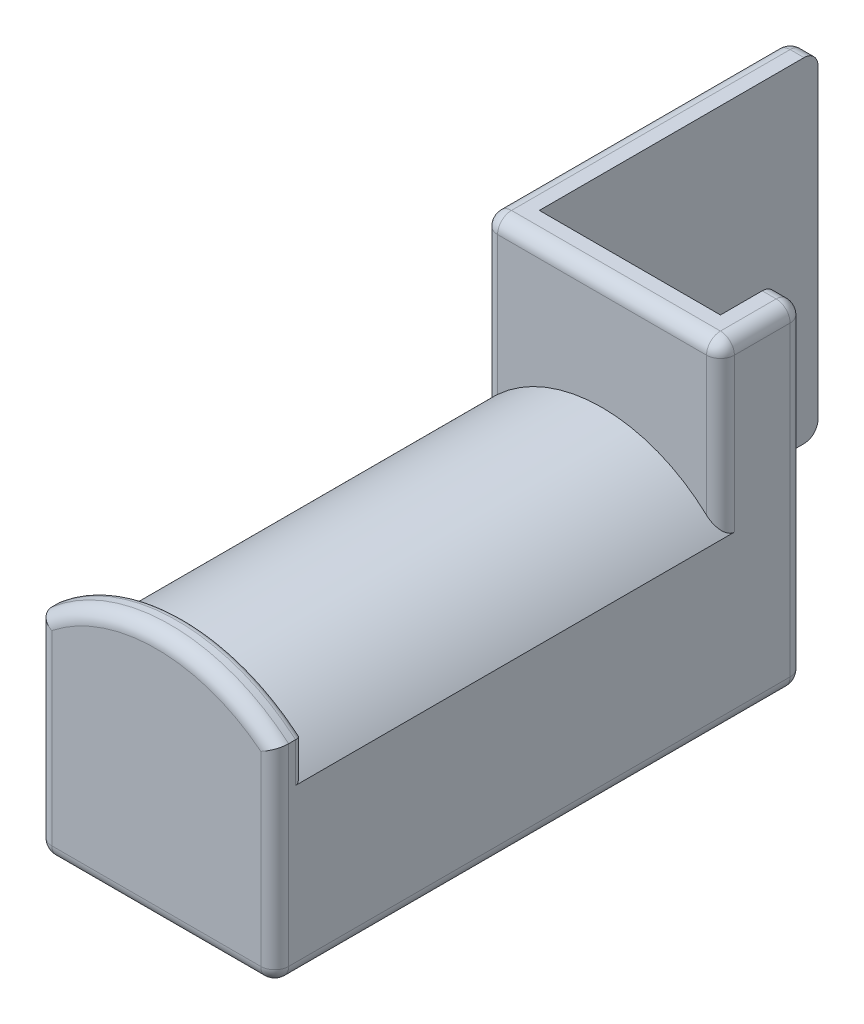
SolidWorks part; units mm, degrees
ref_plane "Front Plane" through (0, 0, 0) normal (0, 0, 1) x (1, 0, 0)
ref_plane "Top Plane" through (0, 0, 0) normal (0, 1, 0) x (1, 0, 0)
ref_plane "Right Plane" through (0, 0, 0) normal (1, 0, 0) x (0, 0, -1)
sketch "Sketch1" plane through (0, 0, 0) normal (0, 1, 0) x (1, 0, 0)
  line L0 (0, 0) -> (0, -34.925)
  line L1 (0, -34.925) -> (26.9875, -34.925)
  line L2 (26.9875, -34.925) -> (26.9875, -25.4)
  line L3 (3.175, 0) -> (3.175, -31.75)
  line L4 (3.175, -31.75) -> (23.8125, -31.75)
  line L5 (23.8125, -31.75) -> (23.8125, -25.4)
  line L6 (0, 0) -> (3.175, 0)
  line L7 (26.9875, -25.4) -> (23.8125, -25.4)
  dimension "D1" = 26.9875
  dimension "D2" = 34.925
  dimension "D3" = 9.525
  dimension "D4" = 3.175
extrude "Boss-Extrude1" add sketch "Sketch1" along normal blind 38.1
sketch "Sketch2" plane through (0, 0, 34.925) normal (0, 0, 1) x (1, 0, 0)
  line L0 (0, 38.1) -> (0, 0) construction
  line L1 (26.9875, 38.1) -> (26.9875, 0) construction
  line L2 (13.4938, 38.1) -> (13.4938, 0) construction
  line L3 (0, 38.1) -> (26.9875, 38.1) construction
  line L4 (0, 0) -> (26.9875, 0) construction
  line L5 (0, 19.05) -> (0, 0)
  line L6 (0, 0) -> (26.9875, 0)
  line L7 (26.9875, 0) -> (26.9875, 19.05)
  arc A0 (0, 19.05) -> (26.9875, 19.05) centre (13.4938, 7.8879) cw
  point P15 (13.4938, 25.4)
  dimension "D1" = 25.4
  dimension "D2" = 6.35
extrude "Boss-Extrude2" add sketch "Sketch2" along normal blind 47.625
sketch "Sketch3" plane through (0, 0, 82.55) normal (0, 0, 1) x (1, 0, 0)
  line L0 (0, 19.05) -> (0, 23.5683)
  line L1 (0, 38.1) -> (0, 19.05) construction
  line L2 (26.9875, 19.05) -> (26.9875, 23.5683)
  line L3 (0, 19.05) -> (0, 0)
  line L4 (0, 0) -> (26.9875, 0)
  line L5 (26.9875, 0) -> (26.9875, 19.05)
  line L6 (0, 19.05) -> (0, 0)
  line L7 (0, 0) -> (26.9875, 0)
  line L8 (26.9875, 0) -> (26.9875, 19.05)
  line L9 (26.9875, 38.1) -> (26.9875, 19.05) construction
  arc A0 (26.9875, 23.5683) -> (0, 23.5683) centre (13.4938, 7.8879) ccw
  arc A1 (26.9875, 19.05) -> (0, 19.05) centre (13.4938, 7.8879) ccw
  arc A2 (26.9875, 19.05) -> (0, 19.05) centre (13.4938, 7.8879) ccw construction
  arc A3 (29.434, 21.0737) -> (-2.4465, 21.0737) centre (13.4938, 7.8879) ccw construction
  dimension "D1" = 0
  dimension "D2" = 3.175
extrude "Boss-Extrude3" add sketch "Sketch3" along normal blind 3.175
fillet "Fillet1" radius 1.5875 17 edges at (26.9875, 28.575, 34.925) (0, 28.575, 34.925) (0, 38.1, 17.4625) (13.4938, 38.1, 34.925) (26.9875, 38.1, 30.1625) (0, 19.05, 0) (26.9875, 19.05, 25.4) (13.4938, 28.575, 85.725) (0, 11.7841, 85.725) (26.9875, 11.7841, 85.725) (13.4938, 0, 85.725) (26.9875, 0, 55.5625) (0, 0, 42.8625) (25.4, 0, 25.4) (25.4, 38.1, 25.4) (1.5875, 0, 0) (1.5875, 38.1, 0)
fillet "Fillet2" radius 0.7937 3 edges at (0, 21.3091, 82.55) (26.9875, 21.3091, 82.55) (13.4938, 28.575, 82.55)
